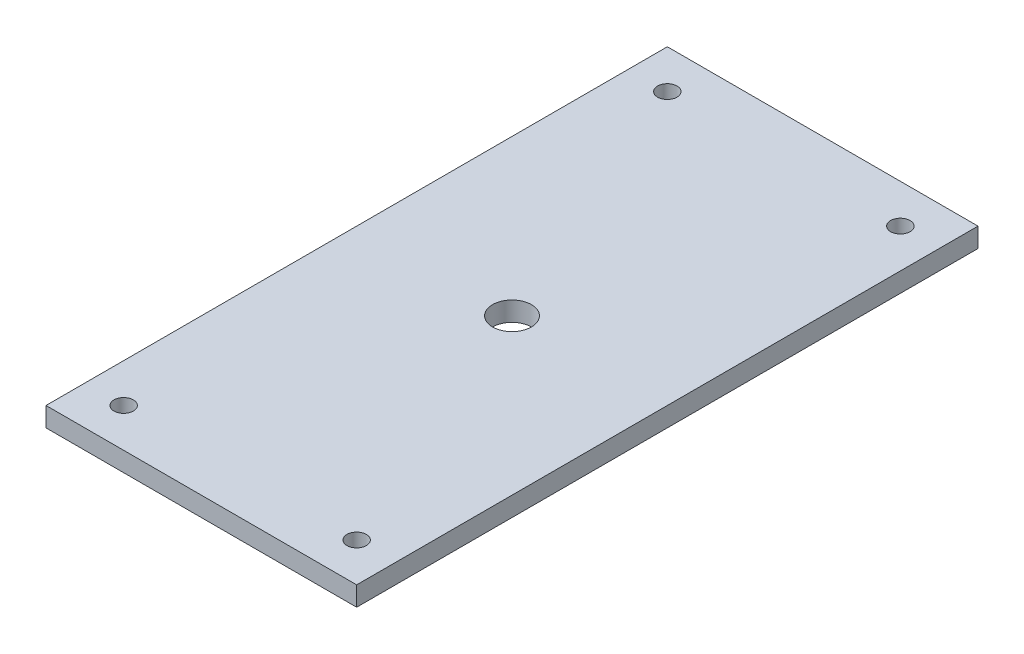
SolidWorks part; units mm, degrees
material "1060 Alloy"
ref_plane "Front Plane" through (0, 0, 0) normal (0, 0, 1) x (1, 0, 0)
ref_plane "Top Plane" through (0, 0, 0) normal (0, 1, 0) x (1, 0, 0)
ref_plane "Right Plane" through (0, 0, 0) normal (1, 0, 0) x (0, 0, -1)
sketch "Sketch1" plane through (0, 0, 0) normal (0, 1, 0) x (1, 0, 0)
  line L0 (-50.8, 50.8) -> (0, 50.8) construction
  line L1 (-25.4, 0) -> (-25.4, 101.6) construction
  line L2 (0, 0) -> (0, 101.6)
  line L3 (0, 101.6) -> (-50.8, 101.6)
  line L4 (-50.8, 0) -> (-50.8, 101.6)
  line L5 (0, 0) -> (-50.8, 0)
  circle A0 centre (-44.45, 6.35) radius 1.5875
  circle A1 centre (-44.45, 95.25) radius 1.5875
  circle A2 centre (-6.35, 6.35) radius 1.5875
  circle A3 centre (-6.35, 95.25) radius 1.5875
  circle A4 centre (-25.4, 50.8) radius 3.175
  dimension "D6" = 3.175
  dimension "D7" = 6.35
  dimension "D3" = 6.35
  dimension "D1" = 101.6
  dimension "D2" = 50.8
  dimension "D8" = 6.35
extrude "Boss-Extrude1" add sketch "Sketch1" along normal blind 3.175
